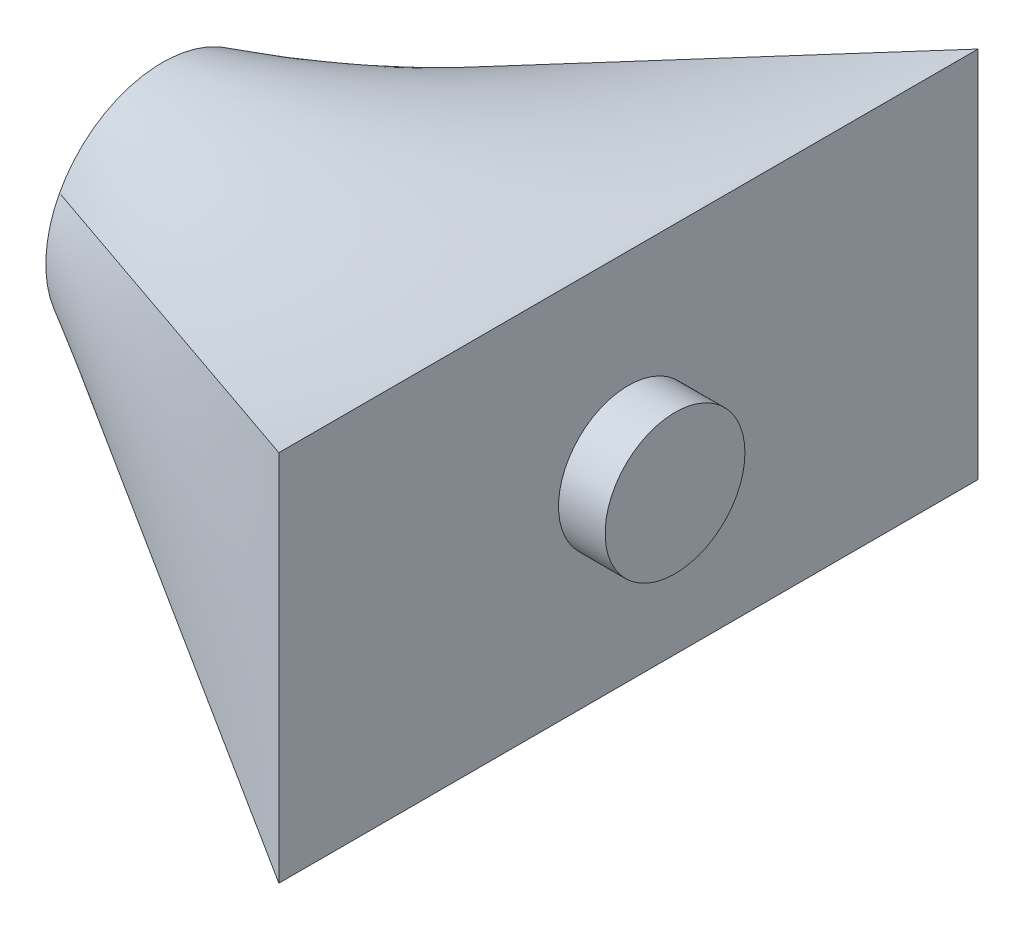
SolidWorks part; units mm, degrees
material "Cast Alloy Steel"
ref_plane "Front Plane" through (0, 0, 0) normal (0, 0, 1) x (1, 0, 0)
ref_plane "Top Plane" through (0, 0, 0) normal (0, 1, 0) x (1, 0, 0)
ref_plane "Right Plane" through (0, 0, 0) normal (1, 0, 0) x (0, 0, -1)
sketch "Sketch1" plane through (0, 0, 0) normal (1, 0, 0) x (0, 0, -1)
  circle A0 centre (0, 0) radius 25
  dimension "D1" = 50
ref_plane "Plane1" through (100, 0, 0) normal (1, 0, 0) x (0, 0, -1)
sketch "Sketch2" plane through (100, 0, 0) normal (1, 0, 0) x (0, 0, -1)
  line L1 (-75, 40) -> (75, 40)
  line L2 (-75, 40) -> (-75, -40)
  line L3 (-75, -40) -> (75, -40)
  line L4 (75, 40) -> (75, -40)
  line L5 (-75, 40) -> (75, -40) construction
  line L6 (-75, -40) -> (75, 40) construction
  point P0 (0, 0)
  dimension "D1" = 150
  dimension "D2" = 80
loft "Loft1" add profiles "Sketch2", "Sketch1"
sketch "Sketch3" plane through (100, 0, 0) normal (1, 0, 0) x (0, 0, -1)
  circle A0 centre (0, 0) radius 15
  dimension "D1" = 30
extrude "Boss-Extrude1" add sketch "Sketch3" along normal blind 10
